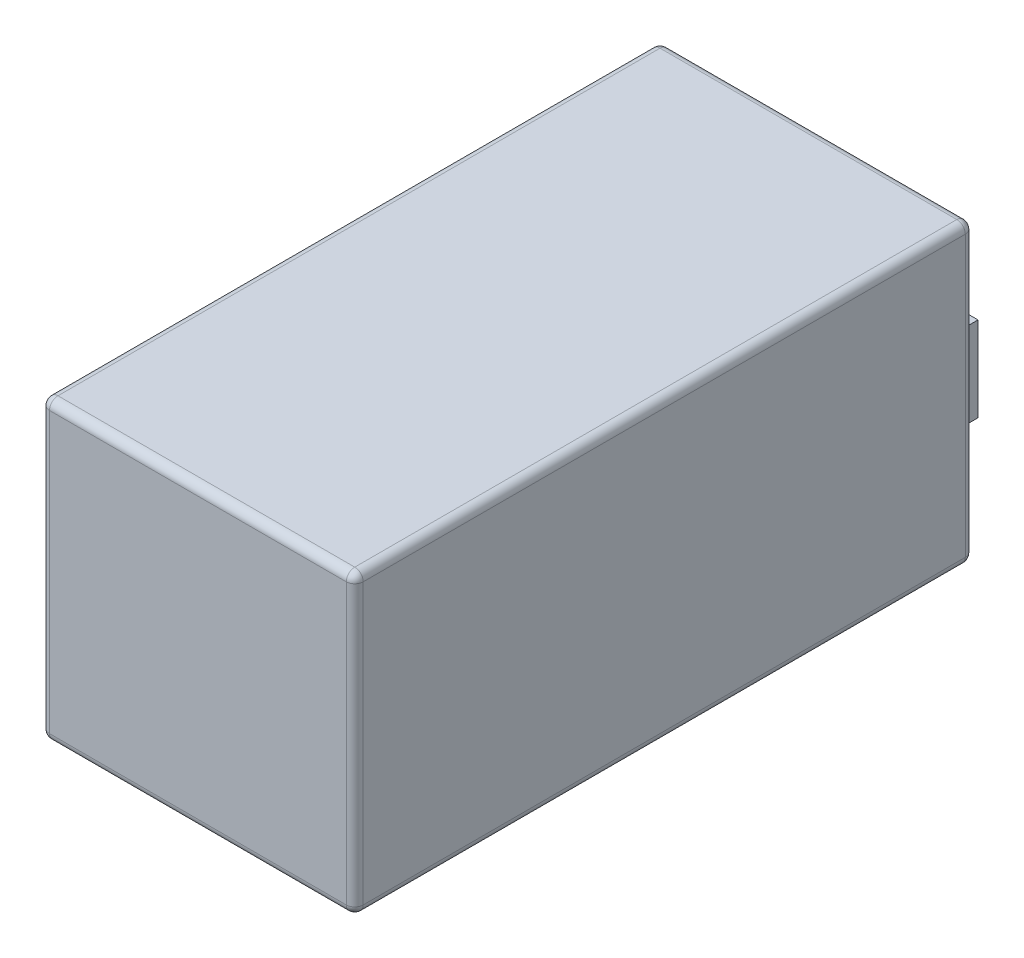
SolidWorks part; units mm, degrees
ref_plane "Front Plane" through (0, 0, 0) normal (0, 0, 1) x (1, 0, 0)
ref_plane "Top Plane" through (0, 0, 0) normal (0, 1, 0) x (1, 0, 0)
ref_plane "Right Plane" through (0, 0, 0) normal (1, 0, 0) x (0, 0, -1)
sketch "Sketch1" plane through (0, 0, 0) normal (0, 1, 0) x (1, 0, 0)
  line L1 (-18.5, -36.5) -> (18.5, -36.5)
  line L2 (-18.5, -36.5) -> (-18.5, 36.5)
  line L3 (-18.5, 36.5) -> (18.5, 36.5)
  line L4 (18.5, -36.5) -> (18.5, 36.5)
  line L5 (-18.5, -36.5) -> (18.5, 36.5) construction
  line L6 (-18.5, 36.5) -> (18.5, -36.5) construction
  point P0 (0, 0)
  dimension "D1" = 37
  dimension "D2" = 73
extrude "Boss-Extrude1" add sketch "Sketch1" along normal mid plane 35
sketch "Sketch2" plane through (0, 0, -36.5) normal (0, 0, -1) x (-1, 0, 0)
  line L1 (-12.5, -5) -> (-16.5, -5)
  line L2 (-12.5, -5) -> (-12.5, 5)
  line L3 (-12.5, 5) -> (-16.5, 5)
  line L4 (-16.5, -5) -> (-16.5, 5)
  line L5 (-12.5, -5) -> (-16.5, 5) construction
  line L6 (-12.5, 5) -> (-16.5, -5) construction
  line L7 (-18.5, 17.5) -> (-18.5, -17.5) construction
  point P0 (-14.5, 0)
  point P7 (0, 0)
  dimension "D1" = 4
  dimension "D2" = 10
  dimension "D3" = 2
extrude "Boss-Extrude2" add sketch "Sketch2" along normal mid plane 5
fillet "Fillet1" radius 1 12 edges at (-18.5, 0, -36.5) (-18.5, 0, 36.5) (0, -17.5, -36.5) (-18.5, -17.5, 0) (0, -17.5, 36.5) (18.5, 0, 36.5) (18.5, 0, -36.5) (18.5, -17.5, 0) (0, 17.5, 36.5) (-18.5, 17.5, 0) (0, 17.5, -36.5) (18.5, 17.5, 0)
